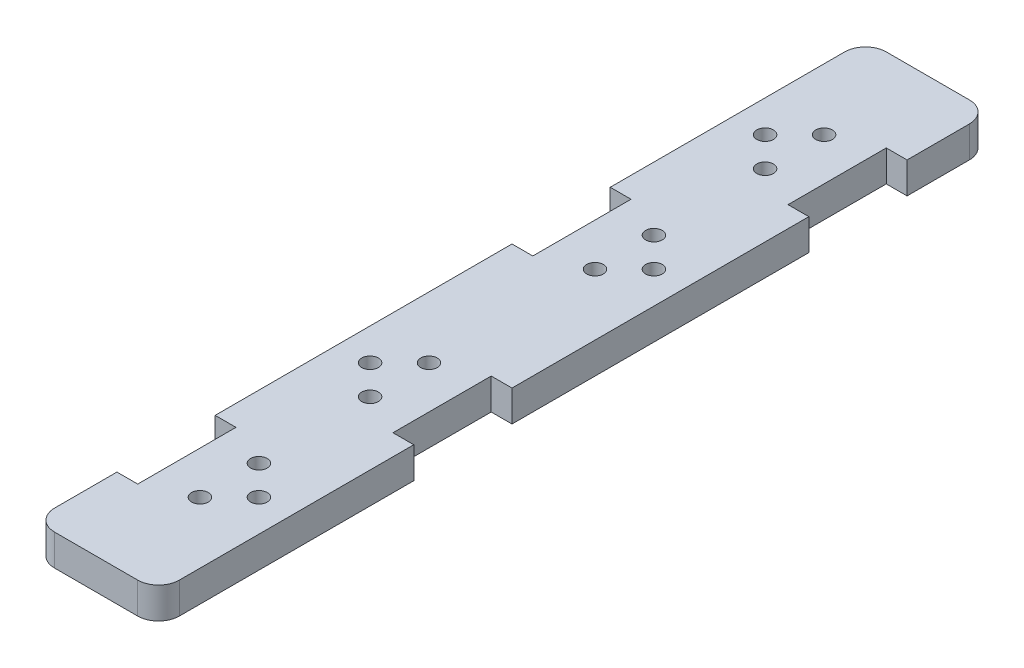
SolidWorks part; units mm, degrees
ref_plane "Front Plane" through (0, 0, 0) normal (0, 0, 1) x (1, 0, 0)
ref_plane "Top Plane" through (0, 0, 0) normal (0, 1, 0) x (1, 0, 0)
ref_plane "Right Plane" through (0, 0, 0) normal (1, 0, 0) x (0, 0, -1)
sketch "Sketch1" plane through (0, 0, 0) normal (0, 1, 0) x (1, 0, 0)
  line L1 (6.35, 0) -> (31.75, 0)
  line L2 (0, 6.35) -> (0, 247.65)
  line L3 (6.35, 254) -> (31.75, 254)
  line L4 (38.1, 6.35) -> (38.1, 247.65)
  arc A0 (0, 6.35) -> (6.35, 0) centre (6.35, 6.35) ccw
  arc A1 (31.75, 0) -> (38.1, 6.35) centre (31.75, 6.35) ccw
  arc A2 (38.1, 247.65) -> (31.75, 254) centre (31.75, 247.65) ccw
  arc A3 (6.35, 254) -> (0, 247.65) centre (6.35, 247.65) ccw
  point P7 (0, 0)
  point P12 (38.1, 254)
  point P15 (0, 254)
  dimension "D3" = 6.35
  dimension "D1" = 38.1
  dimension "D2" = 254
extrude "Boss-Extrude1" add sketch "Sketch1" along normal blind 9.525
sketch "Sketch2" plane through (0, 9.525, 0) normal (0, 1, 0) x (1, 0, 0)
  line L0 (0, 55.4) -> (6.35, 55.4)
  line L1 (0, 55.4) -> (0, 25.4)
  line L2 (0, 25.4) -> (6.35, 25.4)
  line L3 (6.35, 55.4) -> (6.35, 25.4)
  line L4 (6.35, 40.4) -> (63.5487, 40.4) construction
  line L5 (6.35, 0) -> (31.75, 0) construction
  line L6 (0, 247.65) -> (0, 6.35) construction
  line L7 (0, 176.05) -> (6.35, 176.05)
  line L8 (0, 176.05) -> (0, 146.05)
  line L9 (0, 146.05) -> (6.35, 146.05)
  line L10 (6.35, 176.05) -> (6.35, 146.05)
  line L11 (6.35, 161.05) -> (63.5487, 161.05) construction
  line L12 (31.75, 228.6) -> (38.1, 228.6)
  line L13 (31.75, 228.6) -> (31.75, 198.6)
  line L14 (31.75, 198.6) -> (38.1, 198.6)
  line L15 (38.1, 228.6) -> (38.1, 198.6)
  line L16 (38.1, 213.6) -> (-7.3007, 213.6) construction
  line L17 (38.1, 6.35) -> (38.1, 247.65) construction
  line L18 (31.75, 254) -> (6.35, 254) construction
  line L19 (31.75, 107.95) -> (38.1, 107.95)
  line L20 (31.75, 107.95) -> (31.75, 77.95)
  line L21 (31.75, 77.95) -> (38.1, 77.95)
  line L22 (38.1, 107.95) -> (38.1, 77.95)
  line L23 (38.1, 92.95) -> (-7.3007, 92.95) construction
  circle A0 centre (28.35, 40.4) radius 2.54
  circle A1 centre (19.35, 49.4) radius 2.54
  circle A2 centre (19.35, 31.4) radius 2.54
  circle A3 centre (28.35, 161.05) radius 2.54
  circle A4 centre (19.35, 170.05) radius 2.54
  circle A5 centre (19.35, 152.05) radius 2.54
  circle A6 centre (9.75, 213.6) radius 2.54
  circle A7 centre (18.75, 222.6) radius 2.54
  circle A8 centre (18.75, 204.6) radius 2.54
  circle A9 centre (9.75, 92.95) radius 2.54
  circle A10 centre (18.75, 101.95) radius 2.54
  circle A11 centre (18.75, 83.95) radius 2.54
  point P12 (3.175, 25.4)
  dimension "D2" = 5.08
  dimension "D11" = 5.08
  dimension "D16" = 28.35
  dimension "D1" = 30
  dimension "D3" = 19.35
  dimension "D4" = 9
  dimension "D5" = 6.35
  dimension "D6" = 25.4
  dimension "D7" = 28.35
  dimension "D9" = 120.65
  dimension "D10" = 30
  dimension "D12" = 19.35
  dimension "D13" = 9
  dimension "D14" = 6.35
  dimension "D15" = 25.4
  dimension "D18" = 120.65
  dimension "D8" = 2
  dimension "D17" = 2
extrude "Cut-Extrude1" cut sketch "Sketch2" against normal up to next
